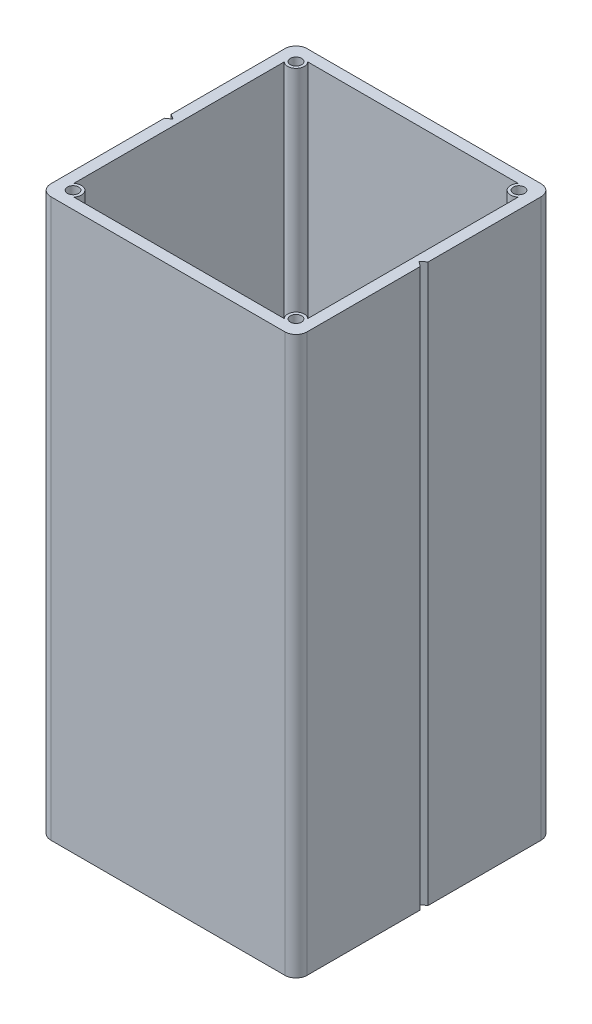
SolidWorks part; units mm, degrees
ref_plane "Front Plane" through (0, 0, 0) normal (0, 0, 1) x (1, 0, 0)
ref_plane "Top Plane" through (0, 0, 0) normal (0, 1, 0) x (1, 0, 0)
ref_plane "Right Plane" through (0, 0, 0) normal (1, 0, 0) x (0, 0, -1)
sketch "Sketch1" plane through (0, 0, 0) normal (0, 1, 0) x (1, 0, 0)
  line L0 (-23, 0.6016) -> (-22.0745, 0)
  line L1 (-23, 23) -> (23, 23)
  line L2 (-23, 23) -> (-23, 0.6016)
  line L3 (-23, -23) -> (23, -23)
  line L4 (23, 23) -> (23, 0.7123)
  line L5 (-23, 23) -> (23, -23) construction
  line L6 (-23, -23) -> (23, 23) construction
  line L7 (-18.882, 21) -> (18.882, 21)
  line L8 (-21, 18.882) -> (-21, -18.882)
  line L9 (-18.882, -21) -> (18.882, -21)
  line L10 (21, 18.882) -> (21, -18.882)
  line L11 (-21, 21) -> (21, -21) construction
  line L12 (-21, -21) -> (21, 21) construction
  line L13 (-22.0745, 0) -> (-23, -0.6016)
  line L14 (23, 0.7123) -> (22.0718, 0)
  line L15 (22.0718, 0) -> (23, -0.7123)
  line L16 (-23, -0.6016) -> (-23, -23)
  line L17 (23, -0.7123) -> (23, -23)
  arc A0 (-18.882, -21) -> (-21, -18.882) centre (-20, -20) ccw
  arc A1 (21, -18.882) -> (18.882, -21) centre (20, -20) ccw
  circle A2 centre (-20, 20) radius 1
  arc A3 (-21, 18.882) -> (-18.882, 21) centre (-20, 20) ccw
  arc A4 (18.882, 21) -> (21, 18.882) centre (20, 20) ccw
  circle A5 centre (20, 20) radius 1
  circle A6 centre (20, -20) radius 1
  circle A7 centre (-20, -20) radius 1
  point P0 (0, 0)
  point P6 (0, 0)
  dimension "D4" = 2
  dimension "D6" = 3
  dimension "D7" = 3
  dimension "D8" = 3
  dimension "D9" = 3
  dimension "D10" = 3
  dimension "D11" = 3
  dimension "D12" = 3
  dimension "D13" = 1.17
  dimension "D1" = 46
  dimension "D2" = 46
  dimension "D3" = 2
  dimension "D5" = 2
extrude "Boss-Extrude1" add sketch "Sketch1" along normal blind 100
fillet "Fillet1" radius 2 2 edges at (23, 50, -23) (-23, 50, -23)
sketch "Sketch3" plane through (0, 0, -23) normal (0, 0, -1) x (-1, 0, 0)
  line L0 (23, 100) -> (23, 0) construction
  line L1 (-23, 0) -> (-23, 100) construction
  line L4 (-21, 100) -> (21, 100) construction
  circle A0 centre (8, 50) radius 1.5
  circle A1 centre (-8, 50) radius 1.5
  dimension "D1" = 16
  dimension "D2" = 15
  dimension "D3" = 15
  dimension "D4" = 50
extrude "Cut-Extrude2" cut sketch "Sketch3" against normal up to next
fillet "Fillet2" radius 2 2 edges at (-23, 50, 23) (23, 50, 23)
